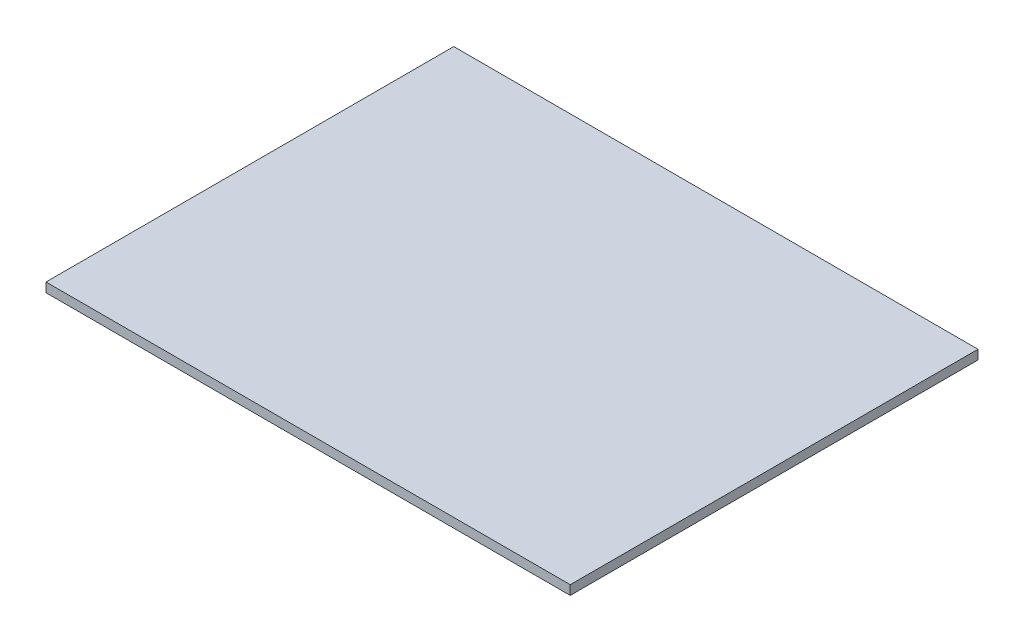
SolidWorks part; units mm, degrees
ref_plane "Front" through (0, 0, 0) normal (0, 0, 1) x (1, 0, 0)
ref_plane "Top" through (0, 0, 0) normal (0, 1, 0) x (1, 0, 0)
ref_plane "Right" through (0, 0, 0) normal (1, 0, 0) x (0, 0, -1)
sketch "Sketch1" plane through (0, 0, 0) normal (0, 1, 0) x (1, 0, 0)
  line L1 (0, 0) -> (90, 0)
  line L2 (0, 0) -> (0, 70)
  line L3 (0, 70) -> (90, 70)
  line L4 (90, 0) -> (90, 70)
  dimension "D1" = 90
  dimension "D2" = 70
extrude "Boss-Extrude1" add sketch "Sketch1" along normal blind 1.6
